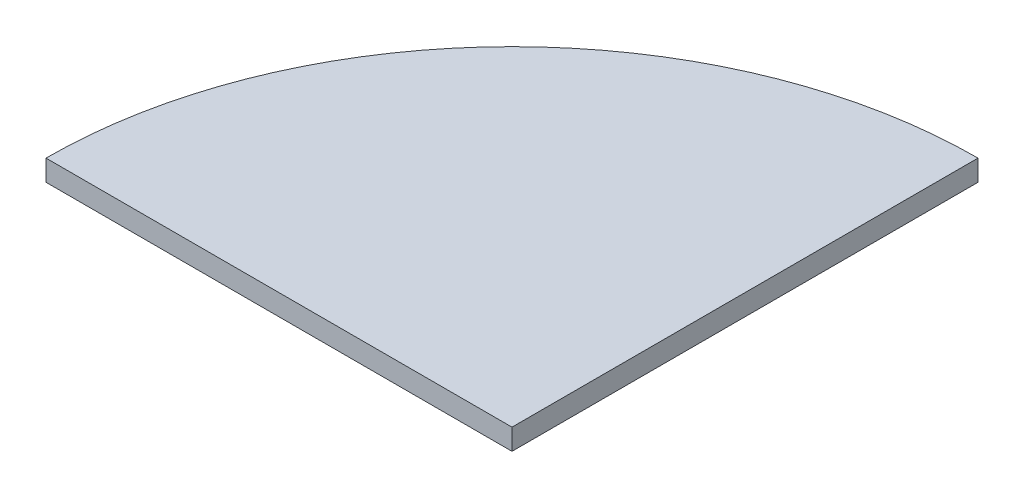
SolidWorks part; units mm, degrees
ref_plane "Спереди" through (0, 0, 0) normal (0, 0, 1) x (1, 0, 0)
ref_plane "Сверху" through (0, 0, 0) normal (0, 1, 0) x (1, 0, 0)
ref_plane "Справа" through (0, 0, 0) normal (1, 0, 0) x (0, 0, -1)
sketch "Эскиз1" plane through (0, 0, 0) normal (0, 1, 0) x (1, 0, 0)
  line L0 (-400, 0) -> (0, 0)
  line L1 (0, 0) -> (0, 400)
  arc A0 (-400, 0) -> (0, 400) centre (0, 0) cw
  dimension "D1" = 400
extrude "Бобышка-Вытянуть1" add sketch "Эскиз1" along normal blind 18
